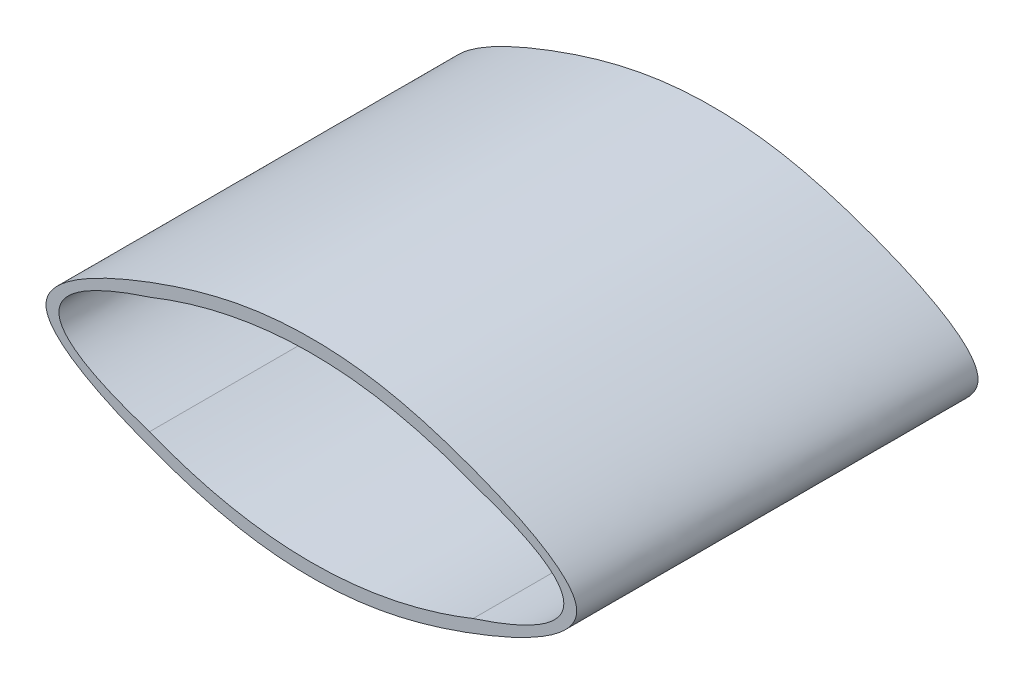
SolidWorks part; units mm, degrees
ref_plane "Front Plane" through (0, 0, 0) normal (0, 0, 1) x (1, 0, 0)
ref_plane "Top Plane" through (0, 0, 0) normal (0, 1, 0) x (1, 0, 0)
ref_plane "Right Plane" through (0, 0, 0) normal (1, 0, 0) x (0, 0, -1)
sketch "Sketch1" plane through (0, 0, 0) normal (0, 0, 1) x (1, 0, 0)
  line L0 (25, 2.5) -> (25, 11.5)
  line L1 (0, 0) -> (25, 0)
  line L5 (0, 2.5) -> (0, 11.5)
  line L6 (12.5, 5) -> (12.5, 14)
  line L7 (25, 7) -> (32, 7) construction
  line L8 (0, 7) -> (-7, 7) construction
  line L9 (12.5, 14) -> (12.5, 15) construction
  line L10 (12.5, 0) -> (12.5, -1) construction
  line L11 (32, 7) -> (33, 7) construction
  line L12 (-7, 7) -> (-8, 7) construction
  line L13 (0, 11.5) -> (0, 12.5) construction
  line L14 (0, 2.5) -> (0, 1.5) construction
  line L15 (25, 11.5) -> (25, 12.5) construction
  line L16 (25, 2.5) -> (25, 1.5) construction
  spline S0 degree 2 poles (0, 2.5) (12.5, -2.5) (25, 2.5) knots 0 0 0 1 1 1
  spline S1 degree 2 poles (0, 11.5) (12.5, 16.5) (25, 11.5) knots 0 0 0 1 1 1
  spline S2 degree 2 poles (0, 2.5) (-14, 7) (0, 11.5) knots 0 0 0 1 1 1
  spline S3 degree 2 poles (25, 11.5) (39, 7) (25, 2.5) knots 0 0 0 1 1 1
  spline S4 degree 3 poles (1.9475, 0.1905) (-12.3006, 7) (1.9475, 13.8095) (12.5, 15.6758) (23.0525, 13.8095) (37.3006, 7) (23.0525, 0.1905) (12.5, -1.6758) (1.9475, 0.1905) (-12.3006, 7) (1.9475, 13.8095) knots -0.391918 -0.25 -0.108082 0 0.108082 0.25 0.391918 0.5 0.608082 0.75 0.891918 1 1.108082 1.25 1.391918 only from (-8, 7) to (-8, 7)
  dimension "D1" = 2.5
  dimension "D2" = 25
  dimension "D3" = 9
  dimension "D4" = 9
  dimension "D5" = 9
  dimension "D6" = 7
  dimension "D7" = 7
  dimension "D8" = 1
  dimension "D9" = 1
  dimension "D10" = 1
  dimension "D11" = 1
  dimension "D12" = 1
  dimension "D13" = 1
  dimension "D14" = 1
  dimension "D15" = 1
  dimension "D16" = 5
extrude "Boss-Extrude1" add sketch "Sketch1" along normal blind 31 contours S4 L1 S0 S2 S1 S3 | S4 L1
sketch "Sketch2" plane through (0, 0, 0) normal (0, 0, -1) x (-1, 0, 0)
  line L0 (-32.9989, 6.9434) -> (7.9989, 6.9434) construction
  line L2 (-17.9989, 14.5025) -> (-17.9989, 4.5025)
  line L3 (-17.9989, 4.5025) -> (-15.9989, 4.5025)
  line L4 (-15.9989, 14.5025) -> (-15.9989, 4.5025)
  line L6 (-9.0011, -0.8011) -> (-9.0011, 9.1989)
  line L7 (-9.0011, 9.1989) -> (-7.0011, 9.1989)
  line L8 (-7.0011, -0.8011) -> (-7.0011, 9.1989)
  line L9 (-15.9989, 14.8011) -> (-15.9989, 14.5025)
  spline S0 degree 3 poles (-1.9475, 0.1905) (12.3006, 7) (-1.9475, 13.8095) (-12.5, 15.6758) (-23.0525, 13.8095) (-37.3006, 7) (-23.0525, 0.1905) (-12.5, -1.6758) (-1.9475, 0.1905) (12.3006, 7) (-1.9475, 13.8095) knots -0.391918 -0.25 -0.108082 0 0.108082 0.25 0.391918 0.5 0.608082 0.75 0.891918 1 1.108082 1.25 1.391918 only from (8, 7) to (8, 7) construction
  spline S1 degree 1 poles (-17.9989, 14.5025) (-15.9989, 14.8011) knots 0 0 1 1
  spline S2 degree 1 poles (-9.0011, -0.8011) (-7.0011, -0.5025) knots 0 0 1 1
  spline M12 degree 2 poles (-25, 11.5) (-12.5, 16.5) (0, 11.5) knots 0 0 0 1 1 1
  spline M14 degree 2 poles (0, 2.5) (-12.5, -2.5) (-25, 2.5) knots 0 0 0 1 1 1
  dimension "D1" = 10
  dimension "D2" = 10
  dimension "D3" = 15
  dimension "D4" = 15
  dimension "D5" = 2
  dimension "D6" = 2
extrude "Boss-Extrude2" add sketch "Sketch2" against normal blind 1 contours S1 L2 L4 L9 M12 | L2 L0 L4 M12 | L0 L2 L3 L4 | L0 L6 L8 M14 | L6 L0 L8 L7 | L6 S2 L8 M14
